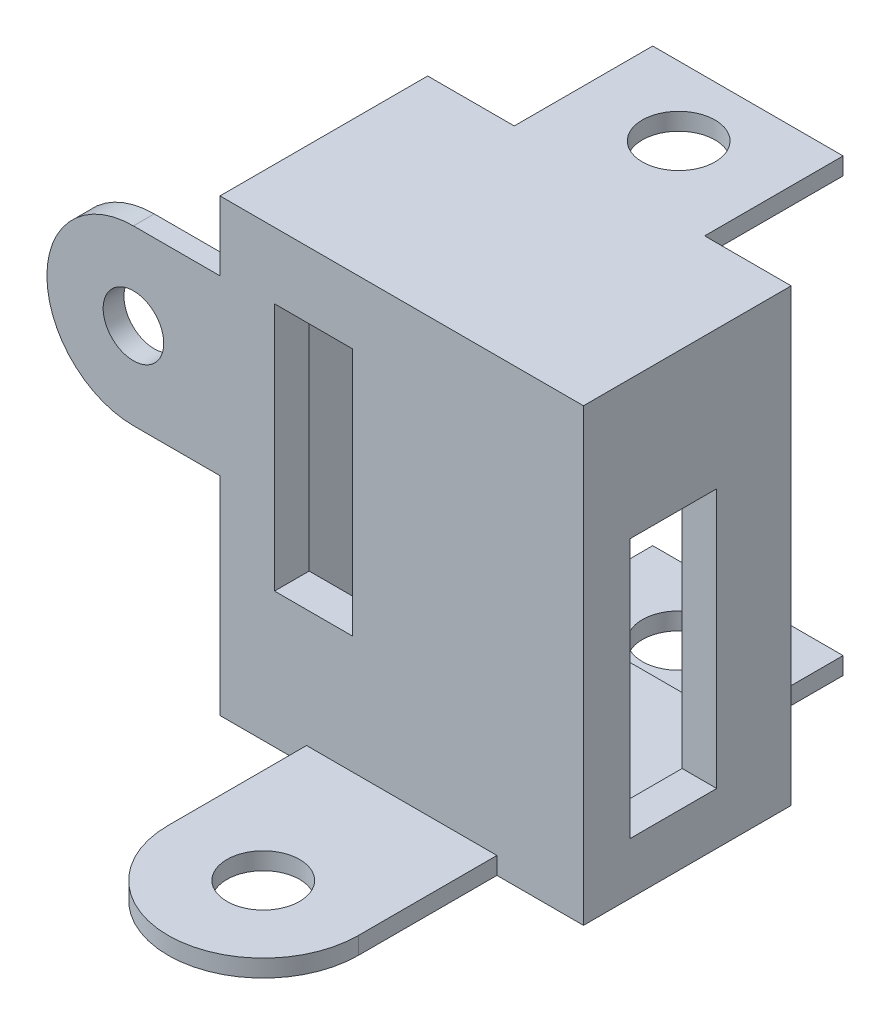
SolidWorks part; units mm, degrees
material "ABS PC"
ref_plane "Front Plane" through (0, 0, 0) normal (0, 0, 1) x (1, 0, 0)
ref_plane "Top Plane" through (0, 0, 0) normal (0, 1, 0) x (1, 0, 0)
ref_plane "Right Plane" through (0, 0, 0) normal (1, 0, 0) x (0, 0, -1)
sketch "Sketch1" plane through (0, 0, 0) normal (0, 0, 1) x (1, 0, 0)
  line L1 (-8.5, -10.5) -> (8.5, -10.5)
  line L2 (-8.5, -10.5) -> (-8.5, 10.5)
  line L3 (-8.5, 10.5) -> (8.5, 10.5)
  line L4 (8.5, -10.5) -> (8.5, 10.5)
  line L5 (-8.5, -10.5) -> (8.5, 10.5) construction
  line L6 (-8.5, 10.5) -> (8.5, -10.5) construction
  line L7 (-10.5, -13) -> (10.5, -13)
  line L8 (-10.5, -13) -> (-10.5, 13)
  line L9 (-10.5, 13) -> (10.5, 13)
  line L10 (10.5, -13) -> (10.5, 13)
  line L11 (-10.5, -13) -> (10.5, 13) construction
  line L12 (-10.5, 13) -> (10.5, -13) construction
  point P0 (0, 0)
  point P5 (0, 0)
  dimension "D1" = 21
  dimension "D2" = 17
  dimension "D3" = 21
  dimension "D4" = 26
extrude "Boss-Extrude1" add sketch "Sketch1" along normal blind 10
sketch "Sketch2" plane through (0, 0, 10) normal (0, 0, 1) x (1, 0, 0)
  line L1 (-10.5, -13) -> (10.5, -13)
  line L2 (-10.5, -13) -> (-10.5, 13)
  line L3 (-10.5, 13) -> (10.5, 13)
  line L4 (10.5, -13) -> (10.5, 13)
  line L5 (-10.5, -13) -> (10.5, 13) construction
  line L6 (-10.5, 13) -> (10.5, -13) construction
  point P0 (0, 0)
  dimension "D1" = 26
  dimension "D2" = 21
extrude "Boss-Extrude2" add sketch "Sketch2" along normal blind 2
sketch "Sketch4" plane through (10.5, 0, 0) normal (1, 0, 0) x (0, 0, -1)
  line L0 (0, 13) -> (-4.3, 13)
  line L1 (-12, 13) -> (0, 13) construction
  line L2 (-4.3, 13) -> (-4.3, 5)
  line L3 (-4.3, 5) -> (-4.3, -10)
  line L4 (-4.3, -10) -> (-9.3, -10)
  line L7 (-9.3, -10) -> (-9.3, 5)
  line L8 (-9.3, 5) -> (-4.3, 5)
  dimension "D1" = 4.3
  dimension "D2" = 8
  dimension "D3" = 15
  dimension "D4" = 5
extrude "Cut-Extrude2" cut sketch "Sketch4" against normal blind 2 contours L8 L7 L4 L3
sketch "Sketch6" plane through (0, 0, 12) normal (0, 0, 1) x (1, 0, 0)
  line L0 (0, 13) -> (5.5, 13)
  line L1 (10.5, 13) -> (-10.5, 13) construction
  line L2 (0, 13) -> (-5.5, 13)
  line L3 (-5.5, 13) -> (-5.5, 18)
  line L4 (5.5, 13) -> (5.5, 18)
  arc A0 (5.5, 18) -> (-5.5, 18) centre (0, 18) ccw
  circle A1 centre (0, 18) radius 1.76
  dimension "D4" = 3.52
  dimension "D1" = 5.5
  dimension "D2" = 5.5
  dimension "D3" = 5
extrude "Boss-Extrude3" add sketch "Sketch6" against normal blind 2
sketch "Sketch9" plane through (0, 0, 12) normal (0, 0, 1) x (1, 0, 0)
  line L0 (0, -13) -> (-5.5, -13)
  line L1 (-10.5, -13) -> (10.5, -13) construction
  line L2 (0, -13) -> (5.5, -13)
  line L3 (5.5, -13) -> (5.5, -18)
  line L4 (-5.5, -13) -> (-5.5, -18)
  arc A0 (-5.5, -18) -> (5.5, -18) centre (0, -18) ccw
  circle A1 centre (0, -18) radius 1.76
  dimension "D5" = 3.52
  dimension "D1" = 5.5
  dimension "D2" = 5.5
  dimension "D3" = 5
  dimension "D4" = 5
extrude "Boss-Extrude5" add sketch "Sketch9" against normal blind 2
sketch "Sketch14" plane through (0, 0, 0) normal (0, 0, -1) x (-1, 0, 0)
  line L0 (-5.5, -13) -> (5.5, -13)
  line L1 (5.5, -13) -> (5.5, -12)
  line L2 (5.5, -12) -> (-5.5, -12)
  line L3 (-5.5, -12) -> (-5.5, -13)
  line L4 (-5.5, 13) -> (5.5, 13)
  line L5 (5.5, 13) -> (5.5, 12)
  line L6 (5.5, 12) -> (-5.5, 12)
  line L7 (-5.5, 12) -> (-5.5, 13)
  dimension "D1" = 1
  dimension "D2" = 1
extrude "Boss-Extrude8" add sketch "Sketch14" along normal blind 8
sketch "Sketch16" plane through (0, 13, 0) normal (0, 1, 0) x (1, 0, 0)
  line L0 (0, 0) -> (0, 4)
  circle A0 centre (0, 4) radius 2.1
  dimension "D2" = 4.2
  dimension "D1" = 4
extrude "Cut-Extrude3" cut sketch "Sketch16" against normal blind 36
sketch "Sketch17" plane through (0, 0, 12) normal (0, 0, 1) x (1, 0, 0)
  line L0 (-10.5, -13) -> (-10.5, -1)
  line L1 (-10.5, 13) -> (-10.5, -13) construction
  line L2 (-10.5, -1) -> (-15.5, -1)
  line L3 (-10.5, -1) -> (-10.5, 9)
  line L4 (-10.5, 9) -> (-15.5, 9)
  arc A0 (-15.5, -1) -> (-15.5, 9) centre (-15.5, 4) cw
  circle A1 centre (-15.5, 4) radius 1.75
  line M10 (-10.5, 13) -> (-10.5, -13)
  dimension "D4" = 3.5
  dimension "D1" = 12
  dimension "D2" = 5
  dimension "D3" = 10
extrude "Boss-Extrude9" add sketch "Sketch17" against normal blind 1.2 contours A0 L2 L4 A1 M10
sketch "Sketch18" plane through (0, 0, 12) normal (0, 0, 1) x (1, 0, 0)
  line L0 (-5.5, 13) -> (5.5, 13)
  line L1 (5.5, 13) -> (5.5, 27.7705)
  line L2 (5.5, 27.7705) -> (-5.5, 27.7705)
  line L3 (-5.5, 27.7705) -> (-5.5, 13)
extrude "Cut-Extrude4" cut sketch "Sketch18" against normal blind 3.2
sketch "Sketch19" plane through (0, 0, 12) normal (0, 0, 1) x (1, 0, 0)
  line L0 (-5.5, -13) -> (5.5, -13)
  line L1 (5.5, -13) -> (5.5, -27.2369)
  line L2 (5.5, -27.2369) -> (-5.5, -27.2369)
  line L3 (-5.5, -27.2369) -> (-5.5, -13)
extrude "Cut-Extrude5" cut sketch "Sketch19" against normal blind 10
sketch "Sketch20" plane through (0, -13, 0) normal (0, -1, 0) x (1, 0, 0)
  line L0 (0, 12) -> (5.5, 12)
  line L1 (-10.5, 12) -> (10.5, 12) construction
  line L2 (0, 12) -> (-5.5, 12)
  line L3 (5.5, 12) -> (5.5, 20)
  line L4 (-5.5, 12) -> (-5.5, 20)
  arc A0 (5.5, 20) -> (-5.5, 20) centre (0, 20) ccw
  circle A1 centre (0, 20) radius 2.1
  dimension "D4" = 4.2
  dimension "D1" = 5.5
  dimension "D2" = 5.5
  dimension "D3" = 8
extrude "Boss-Extrude10" add sketch "Sketch20" against normal blind 1
sketch "Sketch22" plane through (0, 0, 10) normal (0, 0, -1) x (-1, 0, 0)
  line L1 (2.8508, 9.1762) -> (7.3492, 9.1762)
  line L2 (2.8508, 9.1762) -> (2.8508, -5.1967)
  line L3 (2.8508, -5.1967) -> (7.3492, -5.1967)
  line L4 (7.3492, 9.1762) -> (7.3492, -5.1967)
extrude "Cut-Extrude6" cut sketch "Sketch22" against normal blind 10
